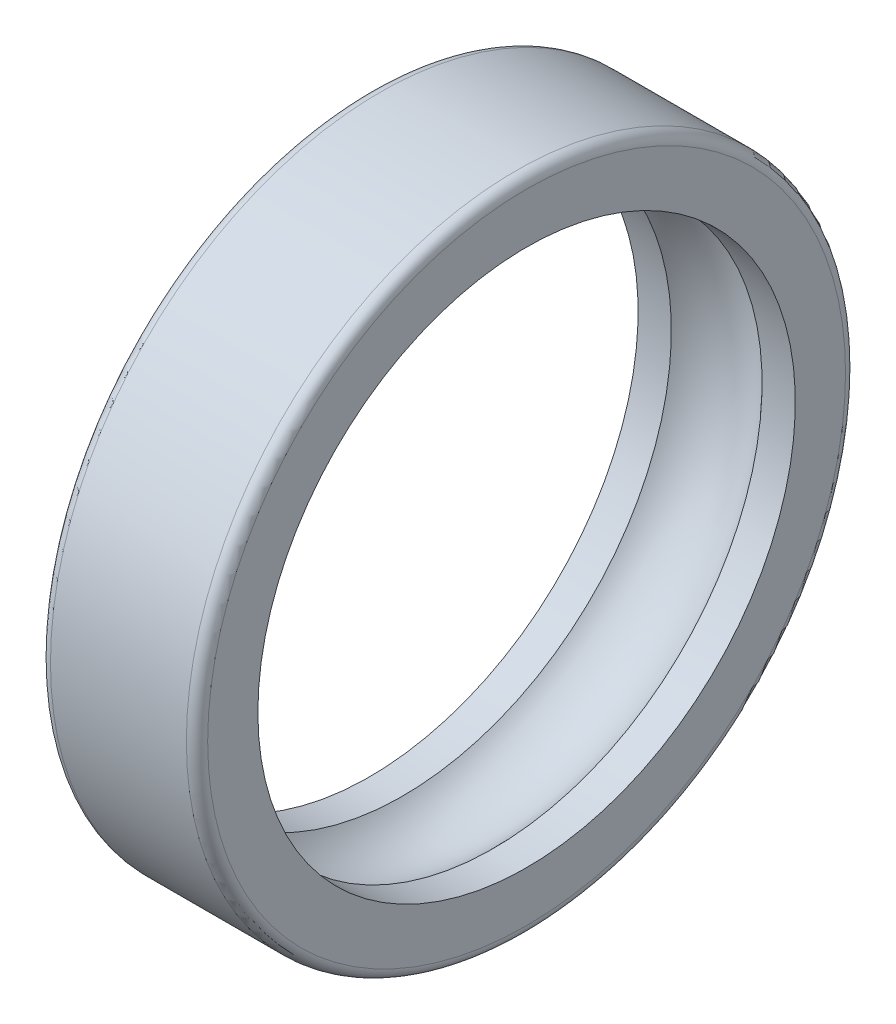
SolidWorks part; units mm, degrees
ref_plane "Front Plane" through (0, 0, 0) normal (0, 0, 1) x (1, 0, 0)
ref_plane "Top Plane" through (0, 0, 0) normal (0, 1, 0) x (1, 0, 0)
ref_plane "Right Plane" through (0, 0, 0) normal (1, 0, 0) x (0, 0, -1)
sketch "Sketch1" plane through (0, 0, 0) normal (0, 0, 1) x (1, 0, 0)
  line L0 (-14.0178, 0) -> (15.5767, 0) construction
  line L1 (0, 59) -> (0, 0) construction
  line L2 (15.5, 65) -> (-15.5, 65)
  line L3 (15.5, 65) -> (15.5, 53)
  line L4 (15.5, 53) -> (8.9443, 53)
  line L5 (-15.5, 65) -> (-15.5, 53)
  line L6 (15.5, 65) -> (-15.5, 53) construction
  line L7 (15.5, 53) -> (-15.5, 65) construction
  line L8 (-8.9443, 53) -> (-15.5, 53)
  arc A0 (8.9443, 53) -> (-8.9443, 53) centre (0, 45) ccw
  point P3 (0, 59)
  dimension "D5" = 12
  dimension "D1" = 31
  dimension "D2" = 53
  dimension "D3" = 65
  dimension "D4" = 8
revolve "Revolve1" add sketch "Sketch1" angle 360 about L0
fillet "Fillet1" radius 2.1 2 edges at (15.5, 0, 65) (-15.5, 0, 65)
